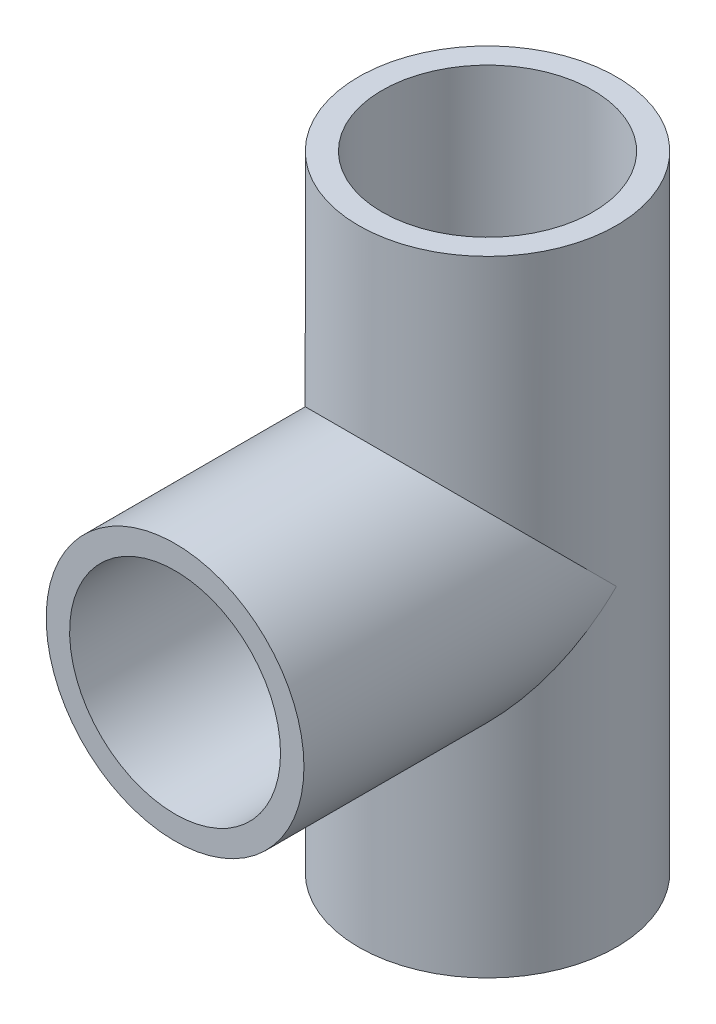
SolidWorks part; units mm, degrees
ref_plane "Front Plane" through (0, 0, 0) normal (0, 0, 1) x (1, 0, 0)
ref_plane "Top Plane" through (0, 0, 0) normal (0, 1, 0) x (1, 0, 0)
ref_plane "Right Plane" through (0, 0, 0) normal (1, 0, 0) x (0, 0, -1)
sketch "Sketch1" plane through (0, 0, 0) normal (0, 1, 0) x (1, 0, 0)
  line L0 (-18.15, 0) -> (18.15, 0) construction
  circle A0 centre (0, 0) radius 13.5
  circle A1 centre (0, 0) radius 16.5
  dimension "D1" = 27
  dimension "D2" = 33
sketch "Sketch3" plane through (0, 0, 0) normal (0, 0, 1) x (1, 0, 0)
  line L0 (0, 0) -> (0, 80)
  line L1 (0, 40) -> (40, 40)
sweep "Sweep2" add profiles "Sketch1" path "Sketch3"
sketch "Sketch4" plane through (0, 0, 0) normal (0, 0, 1) x (1, 0, 0)
  line L0 (-16.5, 40) -> (16.5, 40)
  line L1 (-16.5, 80) -> (-16.5, 0) construction
  line L2 (16.5, 0) -> (16.5, 80) construction
  circle A0 centre (0, 40) radius 16.5
  circle A1 centre (0, 40) radius 13.5
extrude "Boss-Extrude2" add sketch "Sketch4" along normal blind 40 contours A0 | A1
